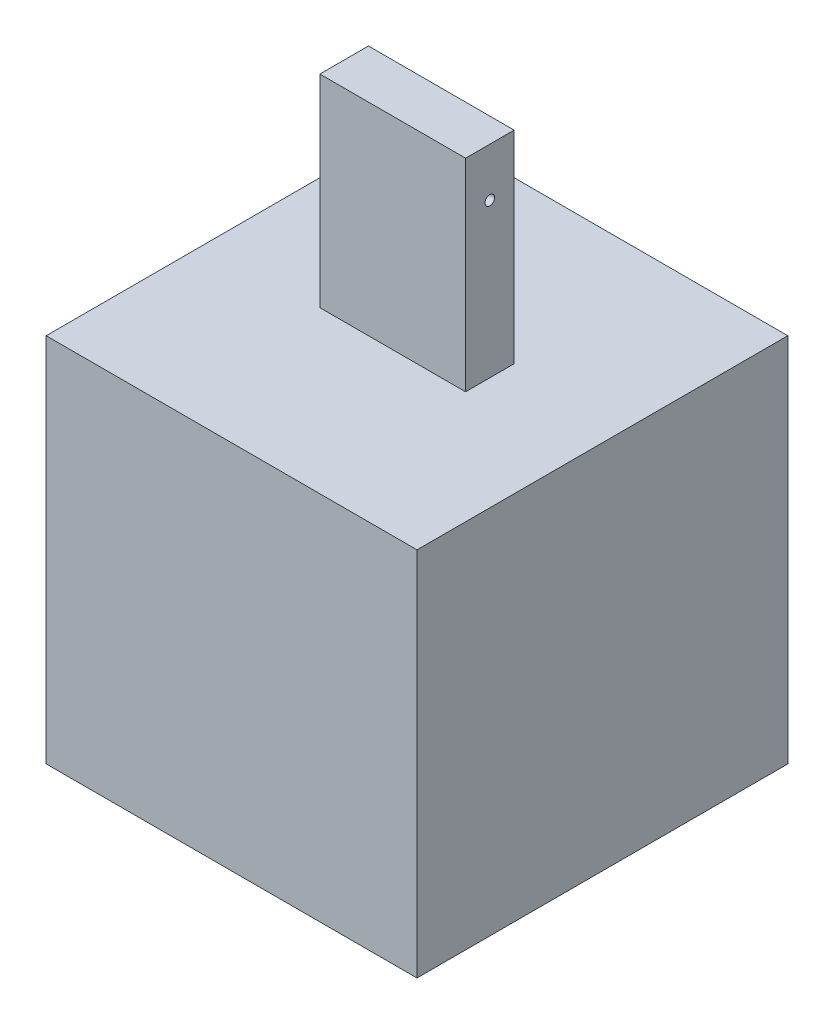
SolidWorks part; units mm, degrees
material "1.0038 (S235JRG2)"
ref_plane "Ön Düzlem" through (0, 0, 0) normal (0, 0, 1) x (1, 0, 0)
ref_plane "Üst Düzlem" through (0, 0, 0) normal (0, 1, 0) x (1, 0, 0)
ref_plane "Sağ Düzlem" through (0, 0, 0) normal (1, 0, 0) x (0, 0, -1)
sketch "Çizim1" plane through (0, 0, 0) normal (0, 0, 1) x (1, 0, 0)
  line L1 (0, 0) -> (458.13, 0)
  line L2 (0, 0) -> (0, 458.13)
  line L3 (0, 458.13) -> (458.13, 458.13)
  line L4 (458.13, 0) -> (458.13, 458.13)
  dimension "D1" = 458.13
  dimension "D2" = 458.13
extrude "Yükseklik-Ekstrüzyon1" add sketch "Çizim1" along normal blind 458.13
sketch "Çizim2" plane through (0, 458.13, 0) normal (0, 1, 0) x (1, 0, 0)
  line L0 (0, -229.065) -> (458.13, -229.065) construction
  line L1 (0, -458.13) -> (0, 0) construction
  line L2 (458.13, -458.13) -> (458.13, 0) construction
  line L3 (458.13, -229.065) -> (229.065, -458.13) construction
  line L4 (458.13, -458.13) -> (0, -458.13) construction
  line L5 (229.065, -458.13) -> (229.065, 0) construction
  line L6 (458.13, 0) -> (0, 0) construction
  line L8 (139.065, -259.065) -> (319.065, -259.065)
  line L9 (139.065, -259.065) -> (139.065, -199.065)
  line L10 (139.065, -199.065) -> (319.065, -199.065)
  line L11 (319.065, -259.065) -> (319.065, -199.065)
  line L12 (139.065, -259.065) -> (319.065, -199.065) construction
  line L13 (139.065, -199.065) -> (319.065, -259.065) construction
  point P12 (229.065, -229.065)
  dimension "D1" = 180
  dimension "D2" = 60
extrude "Yükseklik-Ekstrüzyon2" add sketch "Çizim2" along normal blind 250 separate body
sketch "Çizim3" plane through (139.065, 0, 0) normal (-1, 0, 0) x (0, 0, 1)
  line L1 (199.065, 708.13) -> (259.065, 708.13) construction
  line L2 (259.065, 708.13) -> (259.065, 458.13) construction
  circle A0 centre (229.065, 648.13) radius 6
  dimension "D1" = 12
  dimension "D2" = 30
  dimension "D3" = 60
extrude "Kes-Ekstrüzyon1" cut sketch "Çizim3" against normal blind 299 contours A0
